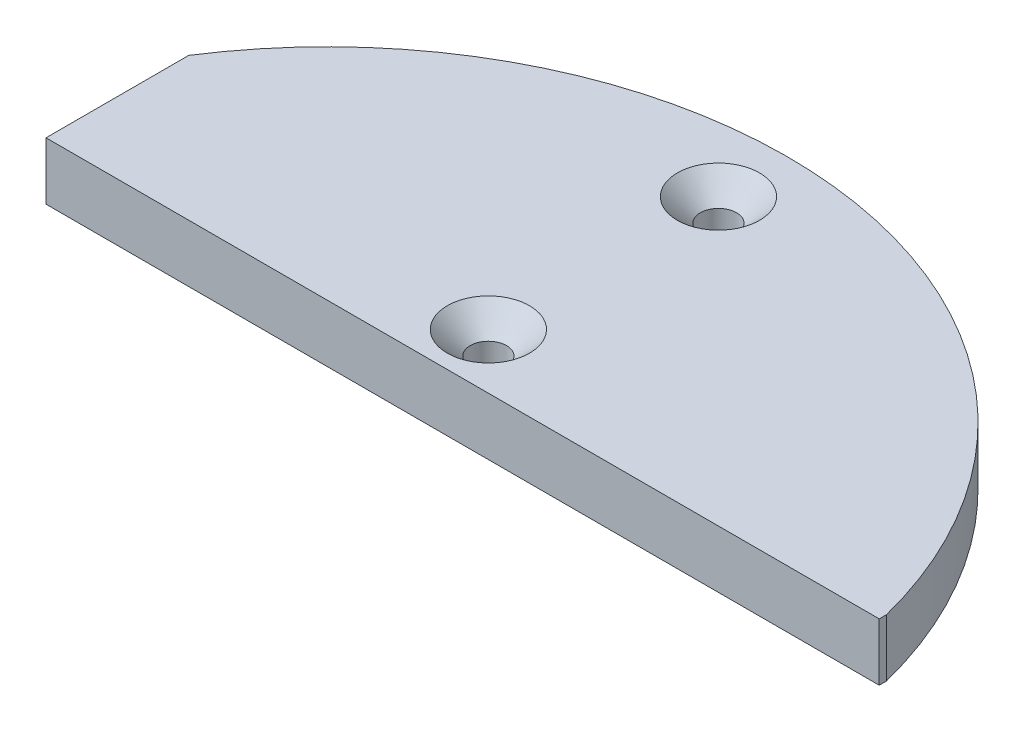
SolidWorks part; units mm, degrees
material "AISI 304"
ref_plane "Front Plane" through (0, 0, 0) normal (0, 0, 1) x (1, 0, 0)
ref_plane "Top Plane" through (0, 0, 0) normal (0, 1, 0) x (1, 0, 0)
ref_plane "Right Plane" through (0, 0, 0) normal (1, 0, 0) x (0, 0, -1)
sketch "Sketch1" plane through (0, 0, 0) normal (0, 1, 0) x (1, 0, 0)
  line L0 (0, 17.78) -> (47.5869, 17.78) construction
  line L1 (0, 17.78) -> (-43, 17.78) construction
  line L2 (0, 17.78) -> (0, 11.43) construction
  line L3 (47.5869, 11.43) -> (49.4974, 11.43)
  line L4 (-43, 11.43) -> (47.5869, 11.43)
  line L5 (-43, 11.43) -> (-43, 50.8)
  line L6 (-43, 50.8) -> (47.5869, 50.8)
  line L7 (47.5869, 11.43) -> (47.5869, 50.8)
  line L8 (49.2434, 11.43) -> (49.2434, 50.546)
  line L9 (49.4974, 11.43) -> (-43, 11.43)
  line L10 (49.4974, 11.43) -> (49.4974, 50.8)
  line L11 (49.4974, 50.8) -> (-43, 50.8)
  line L12 (-43, 11.43) -> (-43, 50.8)
  line L13 (49.2434, 50.546) -> (-43, 50.546)
  line L14 (-42.746, 11.684) -> (47.5869, 11.684)
  line L15 (-42.746, 11.684) -> (-42.746, 50.8)
  line L16 (47.5869, 11.684) -> (49.2434, 11.684)
  circle A0 centre (0, 0) radius 50.8
  circle A1 centre (0, 17.78) radius 2
  circle A2 centre (0, 43.18) radius 2
  dimension "D1" = 101.6
  dimension "D2" = 17.78
  dimension "D4" = 4
  dimension "D5" = 4
  dimension "D3" = 25.4
  dimension "D6" = 6.35
  dimension "D7" = 43
  dimension "D8" = 0.254
  dimension "D9" = 0.254
extrude "Boss-Extrude1" add sketch "Sketch1" along normal blind 6.35 contours L7 A0 L13 L15 L14 A2 A1 | L8 A0 L7 L16 | L13 A0
chamfer "Chamfer1" distance 2.54 angle 45 2 edges at (0, 6.35, -15.78) (0, 6.35, -41.18)
